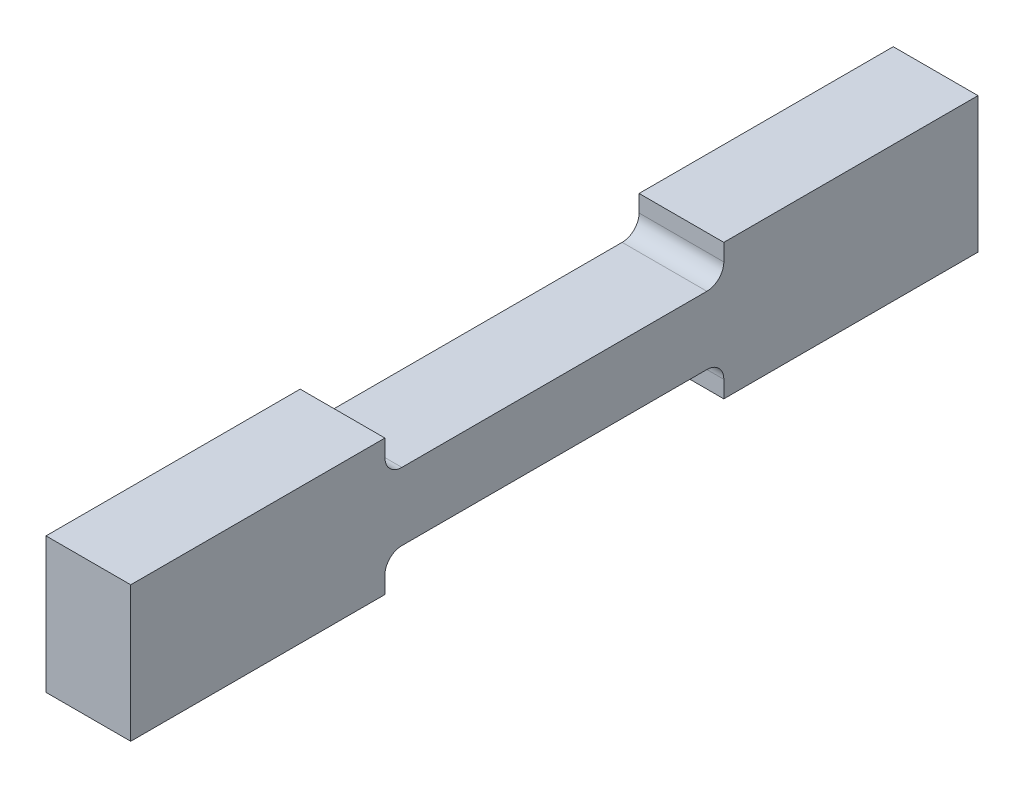
SolidWorks part; units mm, degrees
ref_plane "前视基准面" through (0, 0, 0) normal (0, 0, 1) x (1, 0, 0)
ref_plane "上视基准面" through (0, 0, 0) normal (0, 1, 0) x (1, 0, 0)
ref_plane "右视基准面" through (0, 0, 0) normal (1, 0, 0) x (0, 0, -1)
sketch "草图1" plane through (0, 0, 0) normal (1, 0, 0) x (0, 0, -1)
  line L2 (-5, 1) -> (5, 1)
  line L3 (5, 1) -> (5, 2)
  line L4 (5, 2) -> (12.5, 2)
  line L6 (12.5, -2) -> (12.5, 2)
  line L7 (-5, -1) -> (5, -1)
  line L8 (5, -1) -> (5, -2)
  line L9 (5, -2) -> (12.5, -2)
  line L10 (-5, -1) -> (-5, -2)
  line L11 (-5, -2) -> (-12.5, -2)
  line L12 (-12.5, -2) -> (-12.5, 2)
  line L13 (-5, 2) -> (-12.5, 2)
  line L14 (-5, 1) -> (-5, 2)
  dimension "D4" = 1
  dimension "D5" = 7.5
extrude "凸台-拉伸1" add sketch "草图1" along normal blind 2.5 contours L12 L13 L14 L2 L3 L4 L6 L9 L8 L7 L10 L11
fillet "圆角1" radius 0.5 1 edges at (1.25, 1, -5)
fillet "圆角2" radius 0.5 1 edges at (1.25, -1, -5)
fillet "圆角3" radius 0.5 1 edges at (1.25, 1, 5)
fillet "圆角4" radius 0.5 1 edges at (1.25, -1, 5)
